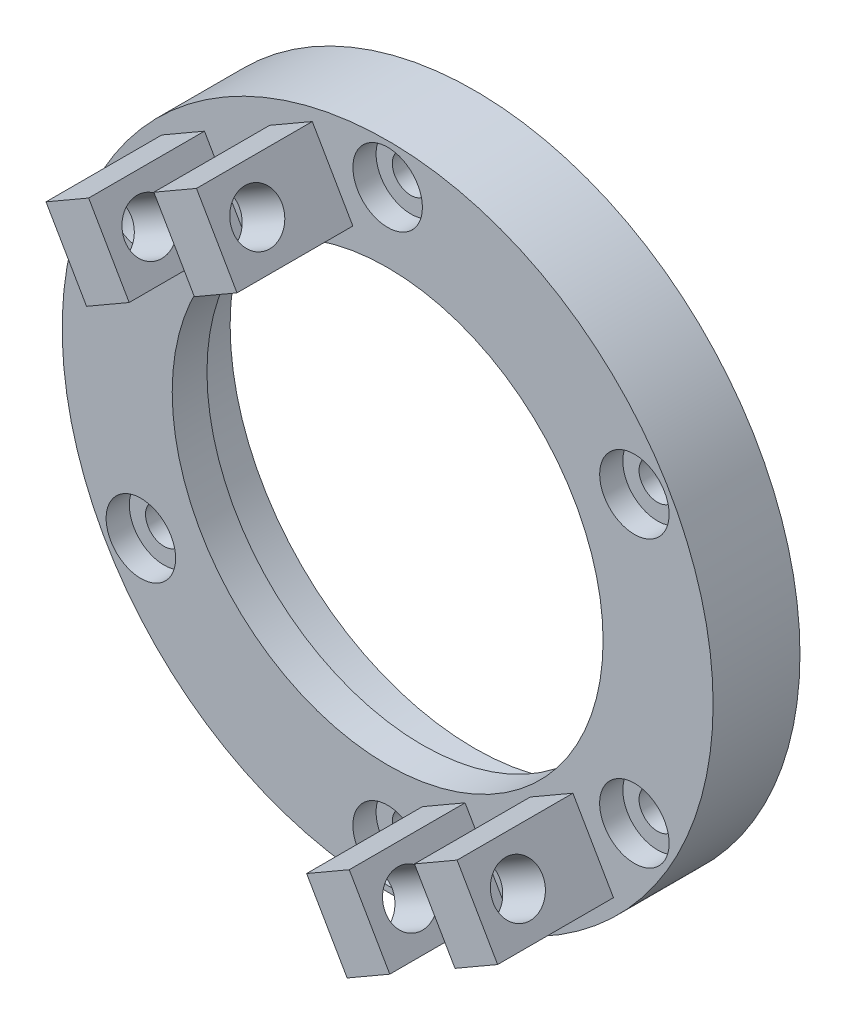
SolidWorks part; units mm, degrees
material "PPE"
ref_plane "Front Plane" through (0, 0, 0) normal (0, 0, 1) x (1, 0, 0)
ref_plane "Top Plane" through (0, 0, 0) normal (0, 1, 0) x (1, 0, 0)
ref_plane "Right Plane" through (0, 0, 0) normal (1, 0, 0) x (0, 0, -1)
sketch "Sketch1" plane through (0, 0, 0) normal (0, 0, 1) x (1, 0, 0)
  circle A0 centre (0, 0) radius 21.1
  circle A1 centre (0, 0) radius 28.1
  dimension "D1" = 42.2
  dimension "D2" = 7
extrude "Boss-Extrude1" add sketch "Sketch1" along normal blind 4.5
sketch "Sketch2" plane through (0, 0, 4.5) normal (0, 0, 1) x (1, 0, 0)
  circle A0 centre (0, 0) radius 18.6
  circle A1 centre (0, 0) radius 28.1
  circle A2 centre (0, 0) radius 21.1 construction
  circle A3 centre (0, 0) radius 28.1 construction
  dimension "D1" = 2.5
extrude "Boss-Extrude2" add sketch "Sketch2" along normal blind 3
hole_wizard "M3 Clearance Hole1" positions "Sketch3" profile "Sketch4" hole size "M3" standard "ANSI Metric" end condition through all
sketch "Sketch3" plane through (0, 0, 0) normal (0, 0, -1) x (-1, 0, 0)
  line L0 (0, 0) -> (0, 21.1) construction
  line L1 (0, 21.1) -> (0, 24.6) construction
  line L2 (0, 24.6) -> (0, 28.1) construction
  circle A0 centre (0, 0) radius 21.1 construction
  circle A1 centre (0, 0) radius 21.1 construction
  circle A2 centre (0, 0) radius 28.1 construction
  point P0 (0, 24.6)
sketch "Sketch4" plane through (0, 24.6, 0) normal (1, 0, 0) x (0, 1, 0)
  line L0 (0, 0) -> (0, 7.5)
  line L1 (0, 7.5) -> (1.6, 7.5)
  line L2 (1.6, 7.5) -> (1.6, 0)
  line L5 (1.6, 0) -> (0, 0)
  line L11 (0, -6.35) -> (0, 107.95) construction
  dimension "Thru Hole Dia." = 3.2
  dimension "Thru Hole Depth" = 7.5
sketch "Sketch6" plane through (0, 0, 7.5) normal (0, 0, 1) x (1, 0, 0)
  circle A0 centre (0, 24.6) radius 3
  dimension "D1" = 6
extrude "Cut-Extrude1" cut sketch "Sketch6" against normal blind 2 contours A0
sketch "Sketch7" plane through (0, 0, 7.5) normal (0, 0, 1) x (1, 0, 0)
  line L0 (0, 0) -> (-11.25, 19.4856) construction
  line L1 (-6.5048, 26.2667) -> (-19.4952, 18.7667)
  line L2 (-19.4952, 18.7667) -> (-15.9952, 12.7045)
  line L3 (-15.9952, 12.7045) -> (-3.0048, 20.2045)
  line L4 (-3.0048, 20.2045) -> (-6.5048, 26.2667)
  line L5 (0, 0) -> (0, 13.2496) construction
  line L6 (-17.7452, 15.7356) -> (-4.7548, 23.2356) construction
  point P8 (-9.5, 16.4545)
  dimension "D1" = 22.5
  dimension "D2" = 30
  dimension "D3" = 7
  dimension "D4" = 15
extrude "Boss-Extrude3" add sketch "Sketch7" along normal blind 10
sketch "Sketch8" plane through (-6.4952, -3.75, 0) normal (-0.866, -0.5, 0) x (0, 0, 1)
  line L0 (14, 22.5) -> (17.5, 22.5) construction
  line L1 (17.5, 26) -> (17.5, 19) construction
  line L2 (17.5, 19) -> (7.5, 19) construction
  line L4 (14, 19) -> (14, 22.5) construction
  circle A0 centre (14, 22.5) radius 2.125
  dimension "D1" = 4.25
extrude "Cut-Extrude2" cut sketch "Sketch8" against normal up to next (15 mm away)
sketch "Sketch9" plane through (-13, 22.5167, 0) normal (-0.5, 0.866, 0) x (0.866, 0.5, 0)
  line L0 (7.5, -7.5) -> (-7.5, -7.5) construction
  line L1 (-3.25, -17.5) -> (3.25, -17.5)
  line L2 (-3.25, -17.5) -> (-3.25, -7.5)
  line L3 (-3.25, -7.5) -> (3.25, -7.5)
  line L4 (3.25, -17.5) -> (3.25, -7.5)
  line L5 (-3.25, -17.5) -> (3.25, -7.5) construction
  line L6 (-3.25, -7.5) -> (3.25, -17.5) construction
  line L7 (7.5, -17.5) -> (-7.5, -17.5) construction
  line L8 (0, 0) -> (0, -12.5) construction
  point P0 (0, -12.5)
  dimension "D1" = 6.5
extrude "Cut-Extrude3" cut sketch "Sketch9" against normal up to next (7 mm away)
pattern_circular "CirPattern1" count 6 over 360 about axis through (0, 0, 0) along (0, 0, 1) of "M3 Clearance Hole1", "Cut-Extrude1"
pattern_circular "CirPattern2" count 2 over 360 about axis through (0, 0, 0) along (0, 0, 1) of "Boss-Extrude3", "Cut-Extrude2", "Cut-Extrude3"
